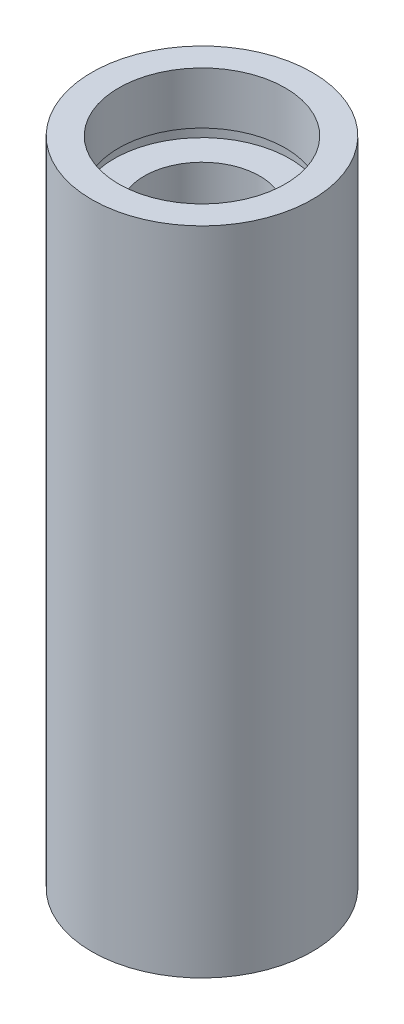
SolidWorks part; units mm, degrees
ref_plane "前视基准面" through (0, 0, 0) normal (0, 0, 1) x (1, 0, 0)
ref_plane "上视基准面" through (0, 0, 0) normal (0, 1, 0) x (1, 0, 0)
ref_plane "右视基准面" through (0, 0, 0) normal (1, 0, 0) x (0, 0, -1)
sketch "草图1" plane through (0, 0, 0) normal (0, 0, 1) x (1, 0, 0)
  line L0 (0, 161.3762) -> (0, 0) construction
  line L1 (141.7365, 0) -> (-131.7984, 0) construction
  line L2 (7, 0) -> (7, 4.5)
  line L3 (7.6, 4.5) -> (7.6, 5.5)
  line L4 (7, 4.5) -> (7.6, 4.5)
  line L5 (5, 5.5) -> (5, 50.8)
  line L6 (5, 5.5) -> (7.6, 5.5)
  line L7 (7.6, 50.8) -> (7.6, 51.8)
  line L8 (5, 50.8) -> (7.6, 50.8)
  line L9 (7.2, 51.8) -> (7.2, 56.3)
  line L10 (7.2, 51.8) -> (7.6, 51.8)
  line L11 (9.525, 0) -> (9.525, 56.3)
  line L12 (7, 0) -> (9.525, 0)
  line L13 (7.2, 56.3) -> (9.525, 56.3)
  dimension "D1" = 7
  dimension "D2" = 4.5
  dimension "D3" = 7.6
  dimension "D4" = 5
  dimension "D5" = 1
  dimension "D6" = 1
  dimension "D7" = 7.2
  dimension "D8" = 4.5
  dimension "D9" = 9.525
  dimension "D10" = 50.8
revolve "旋转1" add sketch "草图1" angle 360 about L0
cosmetic thread "装饰螺纹线1" parameters "D2"=15
cosmetic thread "装饰螺纹线2" parameters "D2"=11
cosmetic thread "装饰螺纹线3" parameters "D2"=15
